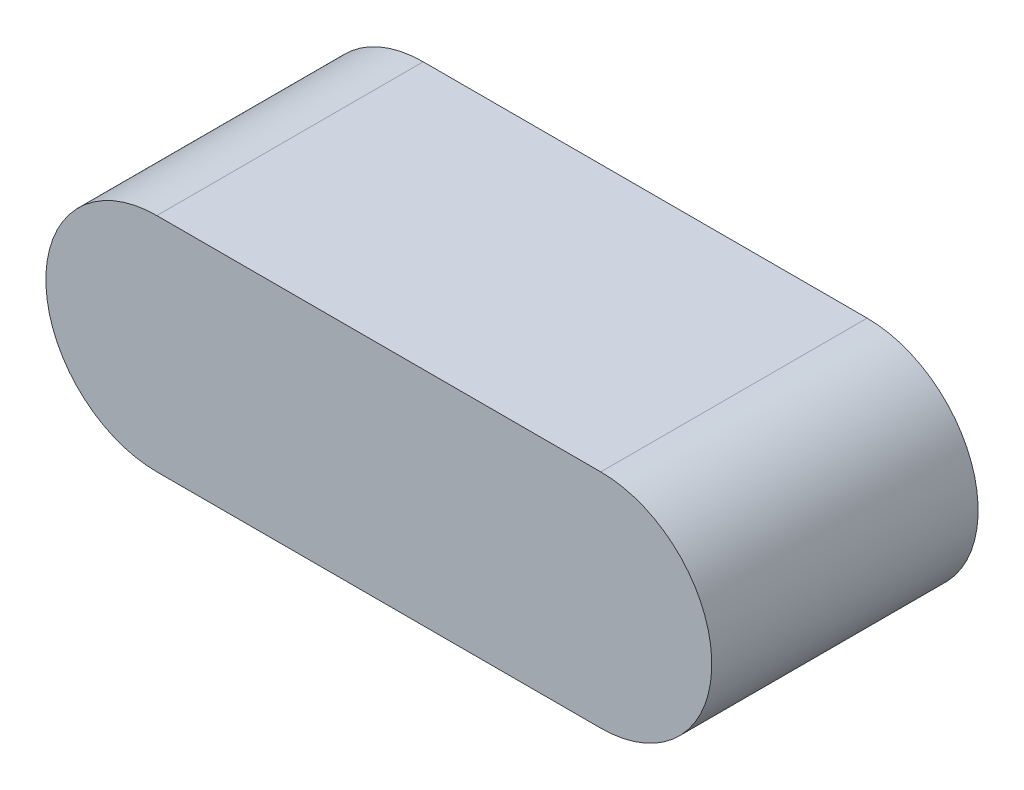
SolidWorks part; units mm, degrees
ref_plane "前视基准面" through (0, 0, 0) normal (0, 0, 1) x (1, 0, 0)
ref_plane "上视基准面" through (0, 0, 0) normal (0, 1, 0) x (1, 0, 0)
ref_plane "右视基准面" through (0, 0, 0) normal (1, 0, 0) x (0, 0, -1)
sketch "草图1" plane through (0, 0, 0) normal (0, 0, 1) x (1, 0, 0)
  line L0 (-12.26, 0) -> (-2.26, 0) construction
  line L1 (-12.26, 2.5) -> (-2.26, 2.5)
  line L2 (-12.26, -2.5) -> (-2.26, -2.5)
  arc A0 (-12.26, 2.5) -> (-12.26, -2.5) centre (-12.26, 0) ccw
  arc A1 (-2.26, -2.5) -> (-2.26, 2.5) centre (-2.26, 0) ccw
  point P3 (-7.26, 0)
  dimension "D1" = 10
  dimension "D2" = 5
extrude "凸台-拉伸1" add sketch "草图1" along normal blind 6
